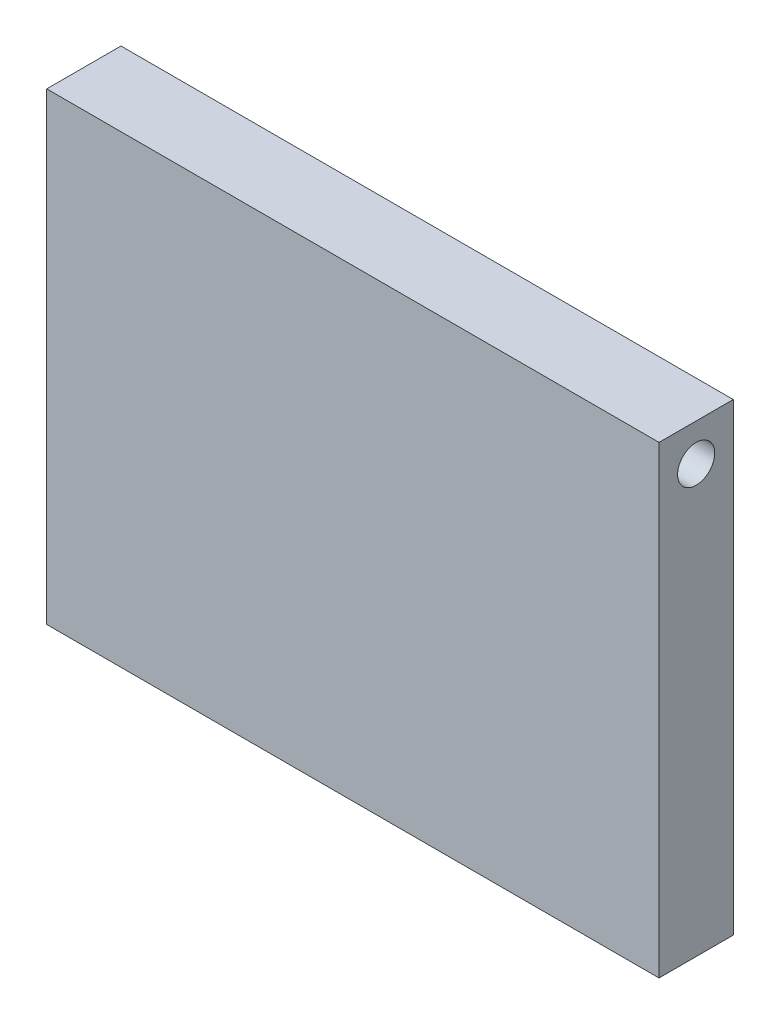
SolidWorks part; units mm, degrees
ref_plane "Alzado" through (0, 0, 0) normal (0, 0, 1) x (1, 0, 0)
ref_plane "Planta" through (0, 0, 0) normal (0, 1, 0) x (1, 0, 0)
ref_plane "Vista lateral" through (0, 0, 0) normal (1, 0, 0) x (0, 0, -1)
sketch "Croquis1" plane through (0, 0, 0) normal (0, 1, 0) x (1, 0, 0)
  line L1 (-16.2139, 2.8136) -> (16.7861, 2.8136)
  line L2 (-16.2139, 2.8136) -> (-16.2139, -1.1864)
  line L3 (-16.2139, -1.1864) -> (16.7861, -1.1864)
  line L4 (16.7861, 2.8136) -> (16.7861, -1.1864)
  dimension "D1" = 33
  dimension "D2" = 4
extrude "Saliente-Extruir1" add sketch "Croquis1" along normal blind 25
sketch "Croquis2" plane through (16.7861, 0, 0) normal (1, 0, 0) x (0, 0, -1)
  line L0 (-1.1864, 25) -> (-1.1864, 0) construction
  line L1 (-1.1864, 25) -> (2.8136, 25) construction
  circle A0 centre (0.8136, 23) radius 1
  dimension "D1" = 2
  dimension "D2" = 2
  dimension "D3" = 2
extrude "Cortar-Extruir1" cut sketch "Croquis2" against normal through all
